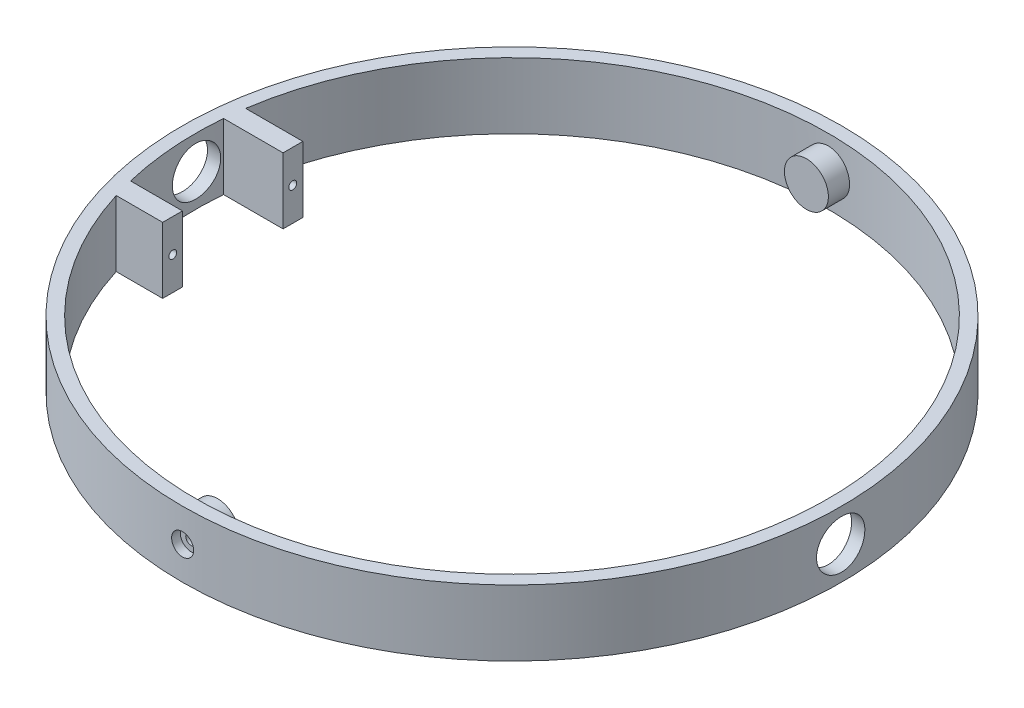
SolidWorks part; units mm, degrees
ref_plane "Front Plane" through (0, 0, 0) normal (0, 0, 1) x (1, 0, 0)
ref_plane "Top Plane" through (0, 0, 0) normal (0, 1, 0) x (1, 0, 0)
ref_plane "Right Plane" through (0, 0, 0) normal (1, 0, 0) x (0, 0, -1)
sketch "Sketch1" plane through (0, 0, 0) normal (0, 1, 0) x (1, 0, 0)
  circle A0 centre (0, 0) radius 72
  circle A1 centre (0, 0) radius 75
  dimension "D1" = 150
  dimension "D2" = 3
extrude "Boss-Extrude1" add sketch "Sketch1" along normal blind 15
sketch "Sketch2" plane through (0, 0, 0) normal (1, 0, 0) x (0, 0, -1)
  circle A0 centre (0, 7.5) radius 5.5
  dimension "D1" = 11
  dimension "D2" = 7.5
extrude "Cut-Extrude1" cut sketch "Sketch2" against normal through all and the other way through all
ref_plane "Plane1" through (0, 0, 73) normal (0, 0, 1) x (1, 0, 0)
sketch "Sketch3" plane through (0, 0, 73) normal (0, 0, 1) x (1, 0, 0)
  circle A0 centre (0, 7.5) radius 5
  dimension "D1" = 10
  dimension "D2" = 7.5
extrude "Boss-Extrude2" add sketch "Sketch3" along normal blind 1 and the other way blind 6 contours A0
mirror "Mirror1" about plane through (0, 0, 0) normal (0, 0, 1) of "Boss-Extrude2"
sketch "Sketch4" plane through (0, 15, 0) normal (0, 1, 0) x (1, 0, 0)
  line L0 (-58.2, -16.8) -> (-70.0126, -16.8)
  line L1 (-58.2, -16.8) -> (-58.2, -21.3)
  line L2 (-58.2, -21.3) -> (-70.0126, -21.3)
  line L3 (-70.0126, -21.3) -> (-70.0126, -16.8)
  line L4 (-58.2, 6.1) -> (-58.2, 10.6)
  line L5 (-58.2, 6.1) -> (-71.7411, 6.1)
  line L6 (-71.7411, 6.1) -> (-71.7411, 10.6)
  line L7 (-71.7411, 10.6) -> (-58.2, 10.6)
  circle A0 centre (0, 0) radius 72 construction
  dimension "D2" = 4.5
  dimension "D3" = 4.5
extrude "Boss-Extrude3" add sketch "Sketch4" against normal up to surface (15 mm away) up to face at (0, 0, 75)
sketch "Sketch5" plane through (-58.2, 0, 0) normal (1, 0, 0) x (0, 0, -1)
  circle A0 centre (8.3, 7.5) radius 0.9
  circle A1 centre (-19, 7.5) radius 0.9
  dimension "D1" = 1.8
  dimension "D2" = 1.8
extrude "Cut-Extrude2" cut sketch "Sketch5" against normal blind 8
sketch "Sketch6" plane through (0, 0, 67) normal (0, 0, -1) x (-1, 0, 0)
  circle A0 centre (0, 7.5) radius 2.45
  dimension "D1" = 4.9
extrude "Cut-Extrude3" cut sketch "Sketch6" against normal blind 4
sketch "Sketch7" plane through (0, 0, 71) normal (0, 0, -1) x (-1, 0, 0)
  circle A0 centre (0, 7.5) radius 1.25
  dimension "D1" = 2.5
extrude "Cut-Extrude4" cut sketch "Sketch7" against normal blind 4
ref_plane "Plane2" through (0, 0, 73) normal (0, 0, -1) x (-1, 0, 0)
sketch "Sketch8" plane through (0, 0, 73) normal (0, 0, -1) x (-1, 0, 0)
  circle A0 centre (0, 7.5) radius 2.5
  dimension "D1" = 5
extrude "Cut-Extrude5" cut sketch "Sketch8" against normal blind 4
